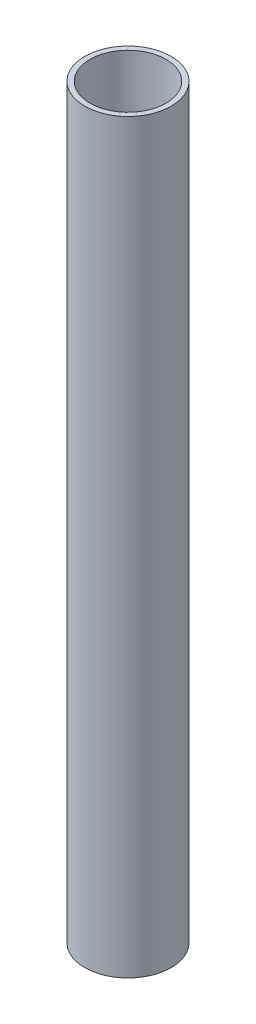
SolidWorks part; units mm, degrees
ref_plane "Front Plane" through (0, 0, 0) normal (0, 0, 1) x (1, 0, 0)
ref_plane "Top Plane" through (0, 0, 0) normal (0, 1, 0) x (1, 0, 0)
ref_plane "Right Plane" through (0, 0, 0) normal (1, 0, 0) x (0, 0, -1)
sketch "Sketch1" plane through (0, 0, 0) normal (0, 1, 0) x (1, 0, 0)
  circle A0 centre (0, 0) radius 22
  circle A1 centre (0, 0) radius 25
  dimension "D1" = 44
  dimension "D2" = 3
extrude "Boss-Extrude1" add sketch "Sketch1" along normal blind 431.8
